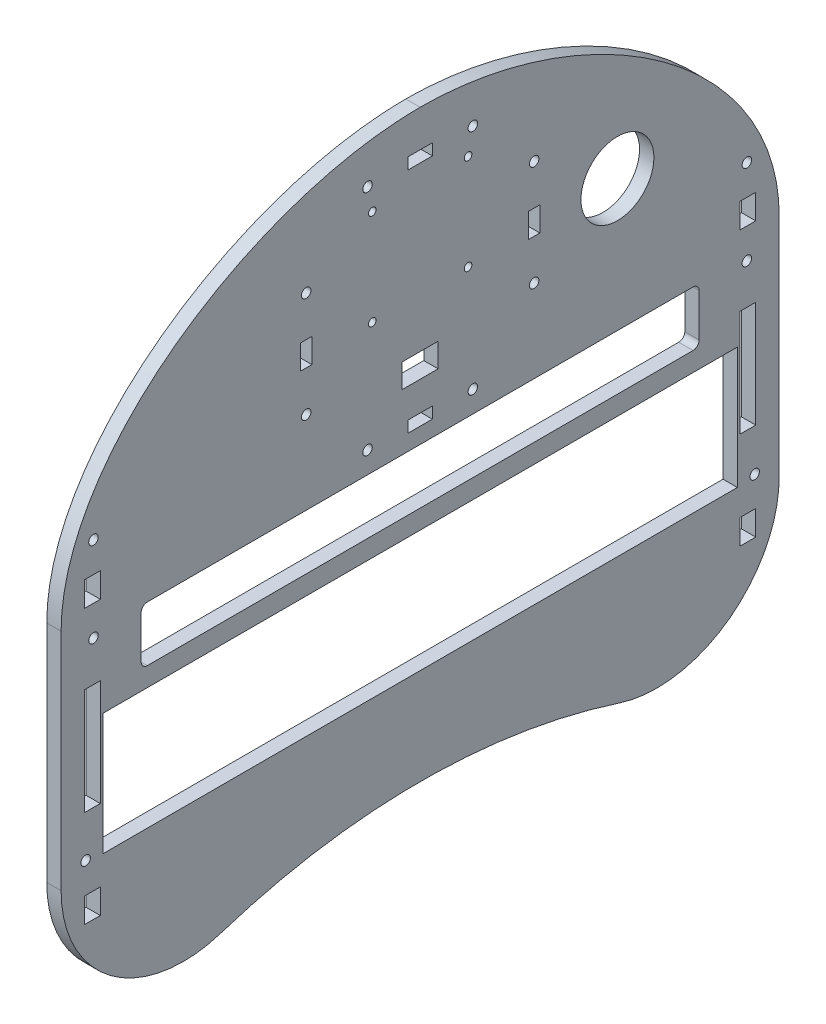
SolidWorks part; units mm, degrees
ref_plane "Front Plane" through (0, 0, 0) normal (0, 0, 1) x (1, 0, 0)
ref_plane "Top Plane" through (0, 0, 0) normal (0, 1, 0) x (1, 0, 0)
ref_plane "Right Plane" through (0, 0, 0) normal (1, 0, 0) x (0, 0, -1)
sketch "Sketch1" plane through (0, 0, 0) normal (1, 0, 0) x (0, 0, -1)
  line L0 (0, 123) -> (0, -402.9766) construction
  line L1 (-150, 8.4066) -> (-150, -102.5888) construction
  line L2 (-132.5, -30) -> (132.5, -30)
  line L3 (-116.54, 1) -> (-116.54, -22)
  line L4 (132.5, -80.8) -> (132.5, -30)
  line L5 (-132.5, -80.8) -> (-132.5, -30)
  line L6 (-116.54, 1) -> (116.54, 1)
  line L7 (136.906, -92.2288) -> (136.906, -102.5888) construction
  line L8 (-116.54, -22) -> (116.54, -22)
  line L9 (116.54, 1) -> (116.54, -22)
  line L10 (-150, 8.4066) -> (-150, -102.5888)
  line L11 (133.631, -92.2288) -> (140.181, -92.2288)
  line L12 (0, -2.4285) -> (0, -37.4285) construction
  line L13 (0, 1) -> (0, 0) construction
  line L14 (133.631, -92.2288) -> (133.631, -102.5888)
  line L15 (133.631, -102.5888) -> (140.181, -102.5888)
  line L16 (140.181, -92.2288) -> (140.181, -102.5888)
  line L17 (133.631, -97.4088) -> (140.181, -97.4088) construction
  line L18 (150, 8.4066) -> (150, -102.5888) construction
  line L19 (132.5, -80.8) -> (-132.5, -80.8)
  line L20 (133.631, -17.6258) -> (140.181, -17.6258)
  line L21 (133.631, -17.6258) -> (133.631, -62.0758)
  line L22 (136.906, -17.6258) -> (136.906, -62.0758) construction
  line L23 (133.631, -62.0758) -> (140.181, -62.0758)
  line L24 (133.631, -39.8508) -> (140.181, -39.8508) construction
  line L25 (140.181, -17.6258) -> (140.181, -62.0758)
  line L26 (140.181, 22.1679) -> (140.181, 11.8079)
  line L28 (133.631, 22.1679) -> (140.181, 22.1679)
  line L29 (133.631, 22.1679) -> (133.631, 11.8079)
  line L30 (133.631, 11.8079) -> (140.181, 11.8079)
  line L31 (133.631, 16.9879) -> (140.181, 16.9879) construction
  line L32 (136.906, 22.1679) -> (136.906, 11.8079) construction
  line L33 (150, 8.4066) -> (150, -102.5888)
  line L36 (-16.764, -82.1415) -> (16.764, -82.1415) construction
  line L38 (0, -82.1415) -> (0, -98.1122) construction
  line L43 (-136.906, 22.1679) -> (-136.906, 11.8079) construction
  line L44 (-133.631, 16.9879) -> (-140.181, 16.9879) construction
  line L45 (-133.631, -39.8508) -> (-140.181, -39.8508) construction
  line L46 (-136.906, -17.6258) -> (-136.906, -62.0758) construction
  line L47 (-133.631, -97.4088) -> (-140.181, -97.4088) construction
  line L48 (-136.906, -92.2288) -> (-136.906, -102.5888) construction
  line L53 (-133.631, 11.8079) -> (-140.181, 11.8079)
  line L54 (-133.631, 22.1679) -> (-133.631, 11.8079)
  line L55 (-133.631, 22.1679) -> (-140.181, 22.1679)
  line L56 (-16.764, -115.5568) -> (16.764, -115.5568) construction
  line L57 (16.764, -82.1415) -> (16.764, -115.5568) construction
  line L58 (-140.181, 22.1679) -> (-140.181, 11.8079)
  line L59 (-16.764, -115.5568) -> (-16.764, -82.1415) construction
  line L60 (-140.181, -17.6258) -> (-140.181, -62.0758)
  line L61 (-133.631, -62.0758) -> (-140.181, -62.0758)
  line L62 (-133.631, -17.6258) -> (-133.631, -62.0758)
  line L63 (-133.631, -17.6258) -> (-140.181, -17.6258)
  line L64 (-140.181, -92.2288) -> (-140.181, -102.5888)
  line L65 (-133.631, -102.5888) -> (-140.181, -102.5888)
  line L66 (-133.631, -92.2288) -> (-133.631, -102.5888)
  line L67 (-133.631, -92.2288) -> (-140.181, -92.2288)
  line L68 (150, -102.5888) -> (126.739, -102.5888) construction
  line L69 (121.1718, -22) -> (145.7704, -22) construction
  line L70 (-139.9293, 97.3753) -> (-139.9293, -115.9494) construction
  line L71 (139.9293, -115.9494) -> (139.9293, 89.0758) construction
  line L72 (-24.6481, 123) -> (24.6481, 123) construction
  line L73 (150, 8.4066) -> (121.1718, 8.4066) construction
  circle A0 centre (16.764, -82.1415) radius 2.54 construction
  circle A1 centre (139.7381, -79.6288) radius 1.9844
  circle A2 centre (136.4742, -0.7921) radius 1.9844
  circle A3 centre (136.4742, 34.7679) radius 1.9844
  circle A4 centre (-136.4742, 34.7679) radius 1.9844
  circle A5 centre (-136.4742, -0.7921) radius 1.9844
  circle A6 centre (-139.7381, -79.6288) radius 1.9844
  arc A8 (-150, -102.5888) -> (150, -102.5888) centre (0, 0) ccw
  circle A12 centre (-16.764, -82.1415) radius 2.54 construction
  circle A13 centre (-16.764, -115.5568) radius 2.54 construction
  circle A14 centre (16.764, -115.5568) radius 2.54 construction
  circle A15 centre (82.4, 56) radius 15.24
  arc A17 (110.1934, -144.5056) -> (-110.1934, -144.5056) centre (0, -390.7576) ccw
  spline S0 degree 3 poles (150, 8.4066) (150, 69.9923) (70.2896, 123) (0, 123) knots 0 0 0 0 1 1 1 1
  spline S1 degree 3 poles (-150, 8.4066) (-150, 69.9923) (-70.2896, 123) (0, 123) knots 0 0 0 0 1 1 1 1
  point P2 (0, -181.7263)
  point P131 (0, -80.8)
  point P132 (0, -30)
  dimension "D12" = 17.78
  dimension "D13" = 17.78
  dimension "D7" = 17.78
  dimension "D25" = 114.3967
  dimension "D17" = 17.78
  dimension "D9" = 17.553
  dimension "D24" = 10.36
  dimension "D4" = 4.406
  dimension "D5" = 50.8
  dimension "D6" = 23
  dimension "D8" = 233.08
  dimension "D10" = 33.528
  dimension "D11" = 33.4153
  dimension "D14" = 34.14
  dimension "D15" = 181.7263
  dimension "D16" = 44.45
  dimension "D18" = 55
  dimension "D19" = 150
  dimension "D20" = 132.5
  dimension "D21" = 8
  dimension "D22" = 123
  dimension "D23" = 30
  dimension "D27" = 6.55
  dimension "D30" = 150
  dimension "D31" = 6.55
  dimension "D32" = 150
extrude "Extrude1" add sketch "Sketch1" along normal blind 5.9944
fillet "Fillet3" radius 50.8 1 edges at (2.9972, -102.5888, 150)
fillet "Fillet4" radius 50.8 1 edges at (2.9972, -144.5056, 110.1934)
fillet "Fillet5" radius 50.8 1 edges at (2.9972, -144.5056, -110.1934)
fillet "Fillet6" radius 50.8 1 edges at (2.9972, -102.5888, -150)
fillet "Fillet12" radius 2.54 1 edges at (2.9972, -22, 116.54)
fillet "Fillet13" radius 2.54 1 edges at (2.9972, 1, 116.54)
fillet "Fillet14" radius 2.54 1 edges at (2.9972, 1, -116.54)
fillet "Fillet15" radius 2.54 1 edges at (2.9972, -22, -116.54)
sketch "Sketch3" plane through (5.9944, 0, 0) normal (1, 0, 0) x (0, 0, -1)
  line L0 (-22, 105.2375) -> (22, 105.2375) construction
  line L1 (-47.6187, 105.2375) -> (47.6187, 105.2375) construction
  line L2 (-47.6187, 105.2375) -> (-47.6187, 10) construction
  line L3 (-47.6187, 10) -> (47.6187, 10) construction
  line L4 (47.6187, 105.2375) -> (47.6187, 10) construction
  line L5 (-47.6187, 105.2375) -> (47.6187, 10) construction
  line L6 (-47.6187, 10) -> (47.6187, 105.2375) construction
  line L7 (45.2375, 52.5187) -> (50, 52.5187)
  line L8 (45.2375, 52.5187) -> (45.2375, 62.7187)
  line L9 (45.2375, 62.7187) -> (50, 62.7187)
  line L10 (50, 52.5187) -> (50, 62.7187)
  line L11 (45.2375, 52.5187) -> (50, 62.7187) construction
  line L12 (45.2375, 62.7187) -> (50, 52.5187) construction
  line L13 (-50, 52.5187) -> (-45.2375, 52.5187)
  line L14 (-50, 52.5187) -> (-50, 62.7187)
  line L15 (-50, 62.7187) -> (-45.2375, 62.7187)
  line L16 (-45.2375, 52.5187) -> (-45.2375, 62.7187)
  line L17 (-50, 52.5187) -> (-45.2375, 62.7187) construction
  line L18 (-50, 62.7187) -> (-45.2375, 52.5187) construction
  line L19 (-5.1, 107.6187) -> (5.1, 107.6187)
  line L20 (-5.1, 107.6187) -> (-5.1, 102.8562)
  line L21 (-5.1, 102.8562) -> (5.1, 102.8562)
  line L22 (5.1, 107.6187) -> (5.1, 102.8562)
  line L23 (-5.1, 107.6187) -> (5.1, 102.8562) construction
  line L24 (-5.1, 102.8562) -> (5.1, 107.6187) construction
  line L25 (-5.1, 12.3812) -> (5.1, 12.3812)
  line L26 (-5.1, 12.3812) -> (-5.1, 7.6187)
  line L27 (-5.1, 7.6187) -> (5.1, 7.6187)
  line L28 (5.1, 12.3812) -> (5.1, 7.6187)
  line L29 (-5.1, 12.3812) -> (5.1, 7.6187) construction
  line L30 (-5.1, 7.6187) -> (5.1, 12.3812) construction
  line L31 (47.6187, 79.6187) -> (47.6187, 35.6187) construction
  line L32 (22, 10) -> (-22, 10) construction
  line L33 (-47.6187, 35.6187) -> (-47.6187, 79.6187) construction
  line L35 (-20, 95.2375) -> (20, 95.2375) construction
  line L36 (-20, 95.2375) -> (-20, 55.2375) construction
  line L37 (-20, 55.2375) -> (20, 55.2375) construction
  line L38 (20, 95.2375) -> (20, 55.2375) construction
  line L39 (-20, 95.2375) -> (20, 55.2375) construction
  line L40 (-20, 55.2375) -> (20, 95.2375) construction
  line L41 (-7.5, 34.6188) -> (7.5, 34.6188)
  line L42 (-7.5, 34.6188) -> (-7.5, 24.6188)
  line L43 (-7.5, 24.6188) -> (7.5, 24.6188)
  line L44 (7.5, 34.6188) -> (7.5, 24.6188)
  line L45 (-7.5, 34.6188) -> (7.5, 24.6188) construction
  line L46 (-7.5, 24.6188) -> (7.5, 34.6188) construction
  circle A0 centre (47.6187, 79.6187) radius 1.9844
  circle A1 centre (47.6187, 35.6187) radius 1.9844
  circle A2 centre (22, 10) radius 1.9844
  circle A3 centre (-22, 10) radius 1.9844
  circle A4 centre (-47.6187, 35.6187) radius 1.9844
  circle A5 centre (-47.6187, 79.6187) radius 1.9844
  circle A6 centre (22, 105.2375) radius 1.9844
  circle A7 centre (-22, 105.2375) radius 1.9844
  circle A8 centre (20, 95.2375) radius 1.5875
  circle A9 centre (20, 55.2375) radius 1.5875
  circle A10 centre (-20, 55.2375) radius 1.5875
  circle A11 centre (-20, 95.2375) radius 1.5875
  point P0 (0, 57.6188)
  point P5 (47.6187, 57.6187)
  point P11 (-47.6187, 57.6187)
  point P16 (0, 105.2375)
  point P21 (0, 10)
  point P42 (0, 75.2375)
  point P51 (0, 29.6188)
  dimension "D6" = 3.9688
  dimension "D8" = 3.175
  dimension "D1" = 95.2375
  dimension "D2" = 10
  dimension "D3" = 10.2
  dimension "D4" = 4.7625
  dimension "D5" = 44
  dimension "D7" = 40
  dimension "D9" = 10
  dimension "D10" = 15
  dimension "D11" = 10
extrude "Cut-Extrude1" cut sketch "Sketch3" against normal blind 10
